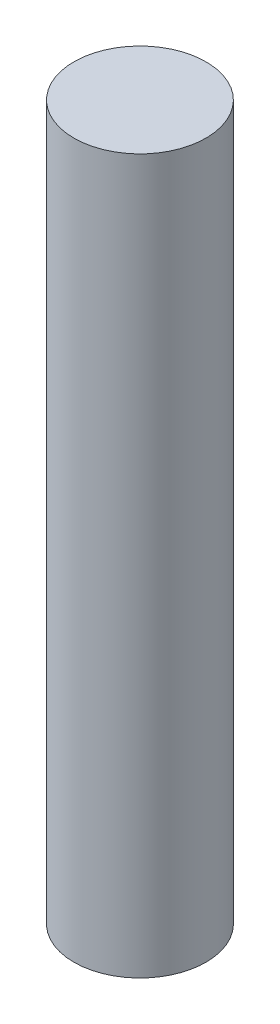
SolidWorks part; units mm, degrees
material "1023 Carbon Steel Sheet (SS)"
ref_plane "Front Plane" through (0, 0, 0) normal (0, 0, 1) x (1, 0, 0)
ref_plane "Top Plane" through (0, 0, 0) normal (0, 1, 0) x (1, 0, 0)
ref_plane "Right Plane" through (0, 0, 0) normal (1, 0, 0) x (0, 0, -1)
sketch "Sketch1" plane through (0, 0, 0) normal (0, 1, 0) x (1, 0, 0)
  circle A0 centre (0, 0) radius 2.5
  dimension "D1" = 5
extrude "Boss-Extrude1" add sketch "Sketch1" along normal mid plane 27
